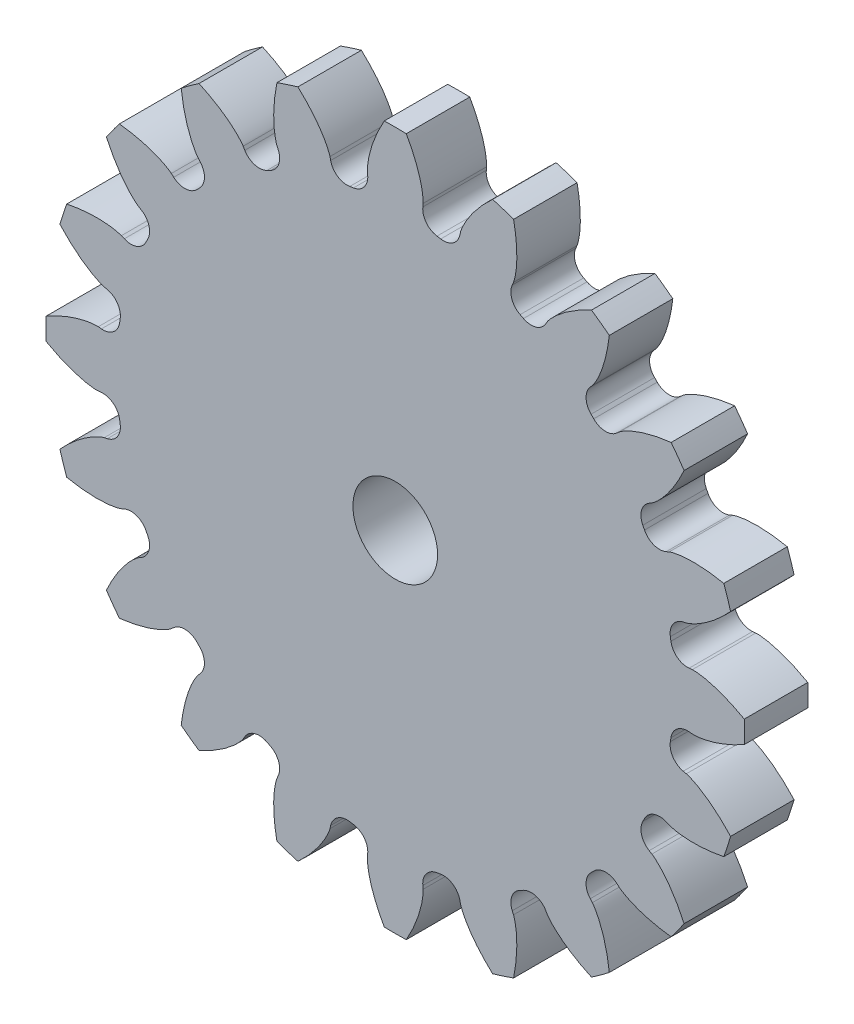
SolidWorks part; units mm, degrees
material "Acrylic (Medium-high impact)"
ref_plane "Front Plane" through (0, 0, 0) normal (0, 0, 1) x (1, 0, 0)
ref_plane "Top Plane" through (0, 0, 0) normal (0, 1, 0) x (1, 0, 0)
ref_plane "Right Plane" through (0, 0, 0) normal (1, 0, 0) x (0, 0, -1)
sketch "Model" plane through (0, 0, 0) normal (0, 0, 1) x (1, 0, 0)
  line L0 (-84.4521, -56.2231) -> (-84.7509, -56.1953)
  line L1 (-84.7509, -61.4561) -> (-84.4521, -61.4283)
  line L2 (-83.8973, -64.9316) -> (-84.19, -64.9974)
  line L3 (-82.5643, -70.0008) -> (-82.2888, -69.882)
  line L4 (-80.6785, -73.0424) -> (-80.9365, -73.1955)
  line L5 (-77.8443, -77.4516) -> (-77.619, -77.2535)
  line L6 (-75.1109, -79.7616) -> (-75.309, -79.9869)
  line L7 (-71.0528, -83.0791) -> (-70.8998, -82.8211)
  line L8 (-67.7394, -84.4314) -> (-67.8582, -84.7069)
  line L9 (-62.8548, -86.3326) -> (-62.789, -86.0399)
  line L10 (-59.2857, -86.5948) -> (-59.3135, -86.8935)
  line L11 (-54.0526, -86.8935) -> (-54.0805, -86.5948)
  line L12 (-50.5772, -86.0399) -> (-50.5113, -86.3326)
  line L13 (-45.508, -84.7069) -> (-45.6268, -84.4314)
  line L14 (-42.4664, -82.8211) -> (-42.3133, -83.0791)
  line L15 (-38.0572, -79.9869) -> (-38.2553, -79.7616)
  line L16 (-35.7472, -77.2535) -> (-35.5219, -77.4516)
  line L17 (-32.4296, -73.1955) -> (-32.6877, -73.0424)
  line L18 (-31.0774, -69.882) -> (-30.8019, -70.0008)
  line L19 (-29.1762, -64.9974) -> (-29.4689, -64.9316)
  line L20 (-28.914, -61.4283) -> (-28.6153, -61.4561)
  line L21 (-28.6153, -56.1953) -> (-28.914, -56.2231)
  line L22 (-29.4689, -52.7198) -> (-29.1762, -52.654)
  line L23 (-30.8019, -47.6506) -> (-31.0774, -47.7694)
  line L24 (-32.6877, -44.609) -> (-32.4296, -44.4559)
  line L25 (-35.5219, -40.1998) -> (-35.7472, -40.3979)
  line L26 (-38.2553, -37.8898) -> (-38.0572, -37.6645)
  line L27 (-42.3133, -34.5722) -> (-42.4664, -34.8303)
  line L28 (-45.6268, -33.22) -> (-45.508, -32.9445)
  line L29 (-50.5113, -31.3188) -> (-50.5772, -31.6115)
  line L30 (-54.0805, -31.0566) -> (-54.0526, -30.7579)
  line L31 (-59.3135, -30.7579) -> (-59.2857, -31.0566)
  line L32 (-62.789, -31.6115) -> (-62.8548, -31.3188)
  line L33 (-67.8582, -32.9445) -> (-67.7394, -33.22)
  line L34 (-70.8998, -34.8303) -> (-71.0528, -34.5722)
  line L35 (-75.309, -37.6645) -> (-75.1109, -37.8898)
  line L36 (-77.619, -40.3979) -> (-77.8443, -40.1998)
  line L37 (-80.9365, -44.4559) -> (-80.6785, -44.609)
  line L38 (-82.2888, -47.7694) -> (-82.5643, -47.6506)
  line L39 (-84.19, -52.654) -> (-83.8973, -52.7198)
  arc A0 (-82.6794, -54.5276) -> (-82.7352, -54.8802) centre (-56.6831, -58.8257) ccw
  arc A1 (-84.4521, -56.2231) -> (-82.7352, -54.8802) centre (-84.3048, -54.6425) ccw
  arc A2 (-89.6666, -57.7836) -> (-89.6666, -59.8678) centre (-56.6831, -58.8257) ccw
  arc A3 (-82.7352, -62.7712) -> (-84.4521, -61.4283) centre (-84.3048, -63.0089) ccw
  arc A4 (-82.7352, -62.7712) -> (-82.6794, -63.1238) centre (-56.6831, -58.8257) ccw
  arc A5 (-83.8973, -64.9316) -> (-82.6794, -63.1238) centre (-84.2456, -63.3828) ccw
  arc A6 (-88.3743, -68.027) -> (-87.7302, -70.0093) centre (-56.6831, -58.8257) ccw
  arc A7 (-80.2409, -70.6287) -> (-82.2888, -69.882) centre (-81.6602, -71.3398) ccw
  arc A8 (-80.2409, -70.6287) -> (-80.0788, -70.9468) centre (-56.6831, -58.8257) ccw
  arc A9 (-80.6785, -73.0424) -> (-80.0788, -70.9468) centre (-81.4884, -71.677) ccw
  arc A10 (-83.9799, -77.3698) -> (-82.7548, -79.0561) centre (-56.6831, -58.8257) ccw
  arc A11 (-75.4406, -77.3307) -> (-77.619, -77.2535) centre (-76.5707, -78.4457) ccw
  arc A12 (-75.4406, -77.3307) -> (-75.1881, -77.5832) centre (-56.6831, -58.8257) ccw
  arc A13 (-75.1109, -79.7616) -> (-75.1881, -77.5832) centre (-76.303, -78.7133) ccw
  arc A14 (-76.9134, -84.8974) -> (-75.2272, -86.1225) centre (-56.6831, -58.8257) ccw
  arc A15 (-68.8041, -82.2214) -> (-70.8998, -82.8211) centre (-69.5344, -83.631) ccw
  arc A16 (-68.8041, -82.2214) -> (-68.486, -82.3835) centre (-56.6831, -58.8257) ccw
  arc A17 (-67.7394, -84.4314) -> (-68.486, -82.3835) centre (-69.1972, -83.8028) ccw
  arc A18 (-67.8667, -89.8729) -> (-65.8844, -90.517) centre (-56.6831, -58.8257) ccw
  arc A19 (-60.9812, -84.822) -> (-62.789, -86.0399) centre (-61.2402, -86.3882) ccw
  arc A20 (-60.9812, -84.822) -> (-60.6286, -84.8778) centre (-56.6831, -58.8257) ccw
  arc A21 (-59.2857, -86.5948) -> (-60.6286, -84.8778) centre (-60.8663, -86.4474) ccw
  arc A22 (-57.7252, -91.8092) -> (-55.6409, -91.8092) centre (-56.6831, -58.8257) ccw
  arc A23 (-52.7376, -84.8778) -> (-54.0805, -86.5948) centre (-52.4998, -86.4474) ccw
  arc A24 (-52.7376, -84.8778) -> (-52.3849, -84.822) centre (-56.6831, -58.8257) ccw
  arc A25 (-50.5772, -86.0399) -> (-52.3849, -84.822) centre (-52.126, -86.3882) ccw
  arc A26 (-47.4817, -90.517) -> (-45.4995, -89.8729) centre (-56.6831, -58.8257) ccw
  arc A27 (-44.8801, -82.3835) -> (-45.6268, -84.4314) centre (-44.169, -83.8028) ccw
  arc A28 (-44.8801, -82.3835) -> (-44.562, -82.2214) centre (-56.6831, -58.8257) ccw
  arc A29 (-42.4664, -82.8211) -> (-44.562, -82.2214) centre (-43.8317, -83.631) ccw
  arc A30 (-38.139, -86.1225) -> (-36.4527, -84.8974) centre (-56.6831, -58.8257) ccw
  arc A31 (-38.178, -77.5832) -> (-38.2553, -79.7616) centre (-37.0631, -78.7133) ccw
  arc A32 (-38.178, -77.5832) -> (-37.9256, -77.3307) centre (-56.6831, -58.8257) ccw
  arc A33 (-35.7472, -77.2535) -> (-37.9256, -77.3307) centre (-36.7955, -78.4457) ccw
  arc A34 (-30.6114, -79.0561) -> (-29.3863, -77.3698) centre (-56.6831, -58.8257) ccw
  arc A35 (-33.2873, -70.9468) -> (-32.6877, -73.0424) centre (-31.8778, -71.677) ccw
  arc A36 (-33.2873, -70.9468) -> (-33.1253, -70.6287) centre (-56.6831, -58.8257) ccw
  arc A37 (-31.0774, -69.882) -> (-33.1253, -70.6287) centre (-31.7059, -71.3398) ccw
  arc A38 (-25.6359, -70.0093) -> (-24.9918, -68.027) centre (-56.6831, -58.8257) ccw
  arc A39 (-30.6868, -63.1238) -> (-29.4689, -64.9316) centre (-29.1206, -63.3828) ccw
  arc A40 (-30.6868, -63.1238) -> (-30.631, -62.7712) centre (-56.6831, -58.8257) ccw
  arc A41 (-28.914, -61.4283) -> (-30.631, -62.7712) centre (-29.0614, -63.0089) ccw
  arc A42 (-23.6995, -59.8678) -> (-23.6995, -57.7836) centre (-56.6831, -58.8257) ccw
  arc A43 (-30.631, -54.8802) -> (-28.914, -56.2231) centre (-29.0614, -54.6425) ccw
  arc A44 (-30.631, -54.8802) -> (-30.6868, -54.5276) centre (-56.6831, -58.8257) ccw
  arc A45 (-29.4689, -52.7198) -> (-30.6868, -54.5276) centre (-29.1206, -54.2686) ccw
  arc A46 (-24.9918, -49.6244) -> (-25.6359, -47.6421) centre (-56.6831, -58.8257) ccw
  arc A47 (-33.1253, -47.0227) -> (-31.0774, -47.7694) centre (-31.7059, -46.3116) ccw
  arc A48 (-33.1253, -47.0227) -> (-33.2873, -46.7046) centre (-56.6831, -58.8257) ccw
  arc A49 (-32.6877, -44.609) -> (-33.2873, -46.7046) centre (-31.8778, -45.9744) ccw
  arc A50 (-29.3863, -40.2816) -> (-30.6114, -38.5953) centre (-56.6831, -58.8257) ccw
  arc A51 (-37.9256, -40.3206) -> (-35.7472, -40.3979) centre (-36.7955, -39.2057) ccw
  arc A52 (-37.9256, -40.3206) -> (-38.178, -40.0682) centre (-56.6831, -58.8257) ccw
  arc A53 (-38.2553, -37.8898) -> (-38.178, -40.0682) centre (-37.0631, -38.9381) ccw
  arc A54 (-36.4527, -32.754) -> (-38.139, -31.5289) centre (-56.6831, -58.8257) ccw
  arc A55 (-44.562, -35.43) -> (-42.4664, -34.8303) centre (-43.8317, -34.0204) ccw
  arc A56 (-44.562, -35.43) -> (-44.8801, -35.2679) centre (-56.6831, -58.8257) ccw
  arc A57 (-45.6268, -33.22) -> (-44.8801, -35.2679) centre (-44.169, -33.8486) ccw
  arc A58 (-45.4995, -27.7785) -> (-47.4817, -27.1344) centre (-56.6831, -58.8257) ccw
  arc A59 (-52.3849, -32.8294) -> (-50.5772, -31.6115) centre (-52.126, -31.2632) ccw
  arc A60 (-52.3849, -32.8294) -> (-52.7376, -32.7736) centre (-56.6831, -58.8257) ccw
  arc A61 (-54.0805, -31.0566) -> (-52.7376, -32.7736) centre (-52.4998, -31.204) ccw
  arc A62 (-55.6409, -25.8422) -> (-57.7252, -25.8422) centre (-56.6831, -58.8257) ccw
  arc A63 (-60.6286, -32.7736) -> (-59.2857, -31.0566) centre (-60.8663, -31.204) ccw
  arc A64 (-60.6286, -32.7736) -> (-60.9812, -32.8294) centre (-56.6831, -58.8257) ccw
  arc A65 (-62.789, -31.6115) -> (-60.9812, -32.8294) centre (-61.2402, -31.2632) ccw
  arc A66 (-65.8844, -27.1344) -> (-67.8667, -27.7785) centre (-56.6831, -58.8257) ccw
  arc A67 (-68.486, -35.2679) -> (-67.7394, -33.22) centre (-69.1972, -33.8486) ccw
  arc A68 (-68.486, -35.2679) -> (-68.8041, -35.43) centre (-56.6831, -58.8257) ccw
  arc A69 (-70.8998, -34.8303) -> (-68.8041, -35.43) centre (-69.5344, -34.0204) ccw
  arc A70 (-75.2272, -31.5289) -> (-76.9134, -32.754) centre (-56.6831, -58.8257) ccw
  arc A71 (-75.1881, -40.0682) -> (-75.1109, -37.8898) centre (-76.303, -38.9381) ccw
  arc A72 (-75.1881, -40.0682) -> (-75.4406, -40.3206) centre (-56.6831, -58.8257) ccw
  arc A73 (-77.619, -40.3979) -> (-75.4406, -40.3206) centre (-76.5707, -39.2057) ccw
  arc A74 (-82.7548, -38.5953) -> (-83.9799, -40.2816) centre (-56.6831, -58.8257) ccw
  arc A75 (-80.0788, -46.7046) -> (-80.6785, -44.609) centre (-81.4884, -45.9744) ccw
  arc A76 (-80.0788, -46.7046) -> (-80.2409, -47.0227) centre (-56.6831, -58.8257) ccw
  arc A77 (-82.2888, -47.7694) -> (-80.2409, -47.0227) centre (-81.6602, -46.3116) ccw
  arc A78 (-87.7302, -47.6421) -> (-88.3743, -49.6244) centre (-56.6831, -58.8257) ccw
  arc A79 (-82.6794, -54.5276) -> (-83.8973, -52.7198) centre (-84.2456, -54.2686) ccw
  circle A80 centre (-56.6831, -58.8257) radius 4
  spline S0 degree 5 poles (-84.7509, -56.1953) (-84.8074, -56.19) (-84.8782, -56.1872) (-84.9775, -56.1898) (-85.1055, -56.1991) (-85.2478, -56.2118) (-85.3901, -56.2258) (-85.5326, -56.2436) (-85.7035, -56.2705) (-85.8744, -56.302) (-86.0736, -56.3427) (-86.2727, -56.3877) (-86.4858, -56.4423) (-86.6986, -56.5012) (-86.9677, -56.5821) (-87.2645, -56.6802) (-87.5744, -56.7917) (-87.9393, -56.9353) (-88.3163, -57.097) (-88.6776, -57.264) (-89.023, -57.4349) (-89.2978, -57.5793) (-89.4893, -57.6839) (-89.6121, -57.7527) (-89.6666, -57.7836) knots 0 0 0 0 0 0 0.057143 0.071429 0.1 0.128571 0.142857 0.2 0.214286 0.271429 0.3 0.342857 0.4 0.428571 0.485714 0.571429 0.642857 0.714286 0.8 0.871429 0.942857 1 1 1 1 1 1 weights 1 1 1 1 1 1 1 1 1 1 1 1 1 1 1 1 1 1 1 1 1 1 1 1 1
  spline S1 degree 5 poles (-89.6666, -59.8678) (-89.4895, -59.9681) (-89.2569, -60.0952) (-88.9681, -60.2456) (-88.6085, -60.4214) (-88.1768, -60.6148) (-87.8691, -60.7439) (-87.5462, -60.8698) (-87.2362, -60.9808) (-86.9677, -61.0691) (-86.7128, -61.1462) (-86.5, -61.2051) (-86.3012, -61.2564) (-86.1305, -61.2962) (-85.9598, -61.3321) (-85.8032, -61.3627) (-85.6465, -61.39) (-85.5041, -61.4118) (-85.3617, -61.4286) (-85.2193, -61.4422) (-85.077, -61.4547) (-84.9491, -61.4627) (-84.864, -61.4639) (-84.7933, -61.4601) (-84.7509, -61.4561) knots -1 -1 -1 -1 -1 -1 -0.814286 -0.757143 -0.7 -0.628571 -0.557143 -0.5 -0.428571 -0.385714 -0.357143 -0.3 -0.285714 -0.228571 -0.214286 -0.185714 -0.142857 -0.128571 -0.085714 -0.071429 -0.042857 0 0 0 0 0 0 weights 1 1 1 1 1 1 1 1 1 1 1 1 1 1 1 1 1 1 1 1 1 1 1 1 1
  spline S2 degree 5 poles (-84.19, -64.9974) (-84.2454, -65.0099) (-84.3136, -65.0291) (-84.4072, -65.0622) (-84.526, -65.1107) (-84.6575, -65.1667) (-84.7885, -65.224) (-84.9185, -65.2849) (-85.0727, -65.3633) (-85.2255, -65.4461) (-85.4025, -65.5464) (-85.5779, -65.6508) (-85.7637, -65.7685) (-85.9479, -65.8903) (-86.1788, -66.0504) (-86.4307, -66.2354) (-86.691, -66.4372) (-86.9937, -66.6865) (-87.3023, -66.9568) (-87.5943, -67.2273) (-87.87, -67.4966) (-88.0867, -67.7188) (-88.2365, -67.8775) (-88.332, -67.9808) (-88.3743, -68.027) knots 0 0 0 0 0 0 0.057143 0.071429 0.1 0.128571 0.142857 0.2 0.214286 0.271429 0.3 0.342857 0.4 0.428571 0.485714 0.571429 0.642857 0.714286 0.8 0.871429 0.942857 1 1 1 1 1 1 weights 1 1 1 1 1 1 1 1 1 1 1 1 1 1 1 1 1 1 1 1 1 1 1 1 1
  spline S3 degree 5 poles (-87.7302, -70.0093) (-87.5308, -70.0499) (-87.2704, -70.0989) (-86.9492, -70.1528) (-86.5528, -70.2088) (-86.0825, -70.2594) (-85.75, -70.287) (-85.404, -70.307) (-85.0749, -70.3167) (-84.7922, -70.3178) (-84.526, -70.3123) (-84.3054, -70.3026) (-84.1004, -70.2899) (-83.9258, -70.275) (-83.7523, -70.2564) (-83.5939, -70.2372) (-83.4365, -70.2147) (-83.2943, -70.1914) (-83.1537, -70.1634) (-83.0141, -70.1323) (-82.8749, -70.1002) (-82.7508, -70.0684) (-82.6695, -70.0431) (-82.6034, -70.0177) (-82.5643, -70.0008) knots -1 -1 -1 -1 -1 -1 -0.814286 -0.757143 -0.7 -0.628571 -0.557143 -0.5 -0.428571 -0.385714 -0.357143 -0.3 -0.285714 -0.228571 -0.214286 -0.185714 -0.142857 -0.128571 -0.085714 -0.071429 -0.042857 0 0 0 0 0 0 weights 1 1 1 1 1 1 1 1 1 1 1 1 1 1 1 1 1 1 1 1 1 1 1 1 1
  spline S4 degree 5 poles (-80.9365, -73.1955) (-80.9853, -73.2244) (-81.0443, -73.2637) (-81.1231, -73.3242) (-81.2211, -73.407) (-81.3288, -73.5009) (-81.4357, -73.5959) (-81.5405, -73.694) (-81.663, -73.8162) (-81.7827, -73.9422) (-81.92, -74.0922) (-82.0546, -74.2457) (-82.1949, -74.4151) (-82.3325, -74.5878) (-82.5026, -74.8115) (-82.685, -75.0653) (-82.8703, -75.3376) (-83.081, -75.6682) (-83.291, -76.0207) (-83.4851, -76.3682) (-83.6641, -76.7095) (-83.8016, -76.9878) (-83.895, -77.185) (-83.9539, -77.3128) (-83.9799, -77.3698) knots 0 0 0 0 0 0 0.057143 0.071429 0.1 0.128571 0.142857 0.2 0.214286 0.271429 0.3 0.342857 0.4 0.428571 0.485714 0.571429 0.642857 0.714286 0.8 0.871429 0.942857 1 1 1 1 1 1 weights 1 1 1 1 1 1 1 1 1 1 1 1 1 1 1 1 1 1 1 1 1 1 1 1 1
  spline S5 degree 5 poles (-82.7548, -79.0561) (-82.5525, -79.0331) (-82.2897, -78.9992) (-81.9676, -78.9511) (-81.5733, -78.8819) (-81.1104, -78.7847) (-80.7856, -78.7082) (-80.4504, -78.6203) (-80.1344, -78.5279) (-79.8652, -78.4415) (-79.6137, -78.3541) (-79.4069, -78.2766) (-79.2159, -78.2012) (-79.0544, -78.1331) (-78.8952, -78.0618) (-78.7505, -77.9946) (-78.6077, -77.9246) (-78.4797, -77.8585) (-78.3546, -77.7883) (-78.2314, -77.7157) (-78.109, -77.6421) (-78.0008, -77.5735) (-77.9313, -77.5243) (-77.8762, -77.4797) (-77.8443, -77.4516) knots -1 -1 -1 -1 -1 -1 -0.814286 -0.757143 -0.7 -0.628571 -0.557143 -0.5 -0.428571 -0.385714 -0.357143 -0.3 -0.285714 -0.228571 -0.214286 -0.185714 -0.142857 -0.128571 -0.085714 -0.071429 -0.042857 0 0 0 0 0 0 weights 1 1 1 1 1 1 1 1 1 1 1 1 1 1 1 1 1 1 1 1 1 1 1 1 1
  spline S6 degree 5 poles (-75.309, -79.9869) (-75.3465, -80.0295) (-75.3904, -80.0851) (-75.4466, -80.167) (-75.5143, -80.276) (-75.5877, -80.3986) (-75.66, -80.522) (-75.7294, -80.6477) (-75.8081, -80.8018) (-75.883, -80.9586) (-75.9672, -81.1437) (-76.0478, -81.3312) (-76.1289, -81.5357) (-76.2063, -81.7425) (-76.2991, -82.0078) (-76.3941, -82.3055) (-76.4861, -82.6217) (-76.5844, -83.0013) (-76.6752, -83.4015) (-76.7524, -83.7919) (-76.8172, -84.1718) (-76.8619, -84.479) (-76.8898, -84.6954) (-76.9064, -84.8352) (-76.9134, -84.8974) knots 0 0 0 0 0 0 0.057143 0.071429 0.1 0.128571 0.142857 0.2 0.214286 0.271429 0.3 0.342857 0.4 0.428571 0.485714 0.571429 0.642857 0.714286 0.8 0.871429 0.942857 1 1 1 1 1 1 weights 1 1 1 1 1 1 1 1 1 1 1 1 1 1 1 1 1 1 1 1 1 1 1 1 1
  spline S7 degree 5 poles (-75.2272, -86.1225) (-75.042, -86.0381) (-74.8025, -85.9247) (-74.511, -85.7795) (-74.1574, -85.5918) (-73.7472, -85.3563) (-73.4619, -85.1832) (-73.1702, -84.996) (-72.8983, -84.8104) (-72.669, -84.6451) (-72.4568, -84.4842) (-72.2841, -84.3467) (-72.1257, -84.2159) (-71.9932, -84.1013) (-71.8638, -83.9843) (-71.7469, -83.8756) (-71.6328, -83.7649) (-71.5314, -83.6625) (-71.4341, -83.5571) (-71.3394, -83.4499) (-71.2457, -83.3422) (-71.164, -83.2434) (-71.1131, -83.1752) (-71.0746, -83.1158) (-71.0528, -83.0791) knots -1 -1 -1 -1 -1 -1 -0.814286 -0.757143 -0.7 -0.628571 -0.557143 -0.5 -0.428571 -0.385714 -0.357143 -0.3 -0.285714 -0.228571 -0.214286 -0.185714 -0.142857 -0.128571 -0.085714 -0.071429 -0.042857 0 0 0 0 0 0 weights 1 1 1 1 1 1 1 1 1 1 1 1 1 1 1 1 1 1 1 1 1 1 1 1 1
  spline S8 degree 5 poles (-67.8582, -84.7069) (-67.8807, -84.759) (-67.9052, -84.8255) (-67.9334, -84.9207) (-67.9641, -85.0453) (-67.996, -85.1846) (-68.0267, -85.3243) (-68.0538, -85.4653) (-68.0811, -85.6361) (-68.1039, -85.8084) (-68.1268, -86.0105) (-68.1454, -86.2138) (-68.1594, -86.4333) (-68.1691, -86.6539) (-68.1753, -86.9348) (-68.1737, -87.2473) (-68.1635, -87.5765) (-68.1397, -87.9679) (-68.1024, -88.3765) (-68.0552, -88.7717) (-67.9994, -89.1531) (-67.947, -89.459) (-67.9066, -89.6735) (-67.8792, -89.8115) (-67.8667, -89.8729) knots 0 0 0 0 0 0 0.057143 0.071429 0.1 0.128571 0.142857 0.2 0.214286 0.271429 0.3 0.342857 0.4 0.428571 0.485714 0.571429 0.642857 0.714286 0.8 0.871429 0.942857 1 1 1 1 1 1 weights 1 1 1 1 1 1 1 1 1 1 1 1 1 1 1 1 1 1 1 1 1 1 1 1 1
  spline S9 degree 5 poles (-65.8844, -90.517) (-65.7343, -90.3795) (-65.5416, -90.1976) (-65.3093, -89.9694) (-65.0309, -89.6817) (-64.7136, -89.3309) (-64.4958, -89.0781) (-64.2762, -88.81) (-64.0749, -88.5494) (-63.908, -88.3214) (-63.7559, -88.1028) (-63.6341, -87.9185) (-63.5239, -87.7453) (-63.4333, -87.5953) (-63.3463, -87.444) (-63.2688, -87.3045) (-63.1944, -87.164) (-63.1297, -87.0352) (-63.0697, -86.905) (-63.0128, -86.7738) (-62.957, -86.6423) (-62.9098, -86.5232) (-62.8824, -86.4426) (-62.8642, -86.3741) (-62.8548, -86.3326) knots -1 -1 -1 -1 -1 -1 -0.814286 -0.757143 -0.7 -0.628571 -0.557143 -0.5 -0.428571 -0.385714 -0.357143 -0.3 -0.285714 -0.228571 -0.214286 -0.185714 -0.142857 -0.128571 -0.085714 -0.071429 -0.042857 0 0 0 0 0 0 weights 1 1 1 1 1 1 1 1 1 1 1 1 1 1 1 1 1 1 1 1 1 1 1 1 1
  spline S10 degree 5 poles (-59.3135, -86.8935) (-59.3188, -86.95) (-59.3216, -87.0208) (-59.319, -87.1201) (-59.3097, -87.2481) (-59.297, -87.3904) (-59.283, -87.5328) (-59.2652, -87.6752) (-59.2383, -87.8461) (-59.2068, -88.017) (-59.1661, -88.2162) (-59.121, -88.4154) (-59.0665, -88.6284) (-59.0076, -88.8413) (-58.9267, -89.1104) (-58.8286, -89.4071) (-58.7171, -89.717) (-58.5735, -90.0819) (-58.4118, -90.459) (-58.2447, -90.8202) (-58.0738, -91.1657) (-57.9295, -91.4404) (-57.8248, -91.632) (-57.7561, -91.7547) (-57.7252, -91.8092) knots 0 0 0 0 0 0 0.057143 0.071429 0.1 0.128571 0.142857 0.2 0.214286 0.271429 0.3 0.342857 0.4 0.428571 0.485714 0.571429 0.642857 0.714286 0.8 0.871429 0.942857 1 1 1 1 1 1 weights 1 1 1 1 1 1 1 1 1 1 1 1 1 1 1 1 1 1 1 1 1 1 1 1 1
  spline S11 degree 5 poles (-55.6409, -91.8092) (-55.5407, -91.6321) (-55.4136, -91.3996) (-55.2631, -91.1107) (-55.0874, -90.7511) (-54.8939, -90.3194) (-54.7649, -90.0117) (-54.6389, -89.6888) (-54.528, -89.3788) (-54.4397, -89.1103) (-54.3626, -88.8554) (-54.3037, -88.6426) (-54.2524, -88.4438) (-54.2126, -88.2731) (-54.1767, -88.1024) (-54.1461, -87.9458) (-54.1188, -87.7891) (-54.097, -87.6467) (-54.0802, -87.5043) (-54.0666, -87.3619) (-54.0541, -87.2196) (-54.046, -87.0917) (-54.0449, -87.0066) (-54.0487, -86.9359) (-54.0526, -86.8935) knots -1 -1 -1 -1 -1 -1 -0.814286 -0.757143 -0.7 -0.628571 -0.557143 -0.5 -0.428571 -0.385714 -0.357143 -0.3 -0.285714 -0.228571 -0.214286 -0.185714 -0.142857 -0.128571 -0.085714 -0.071429 -0.042857 0 0 0 0 0 0 weights 1 1 1 1 1 1 1 1 1 1 1 1 1 1 1 1 1 1 1 1 1 1 1 1 1
  spline S12 degree 5 poles (-50.5113, -86.3326) (-50.4989, -86.388) (-50.4797, -86.4562) (-50.4465, -86.5498) (-50.3981, -86.6686) (-50.342, -86.8001) (-50.2847, -86.9311) (-50.2239, -87.0611) (-50.1455, -87.2154) (-50.0626, -87.3681) (-49.9624, -87.5451) (-49.858, -87.7205) (-49.7402, -87.9063) (-49.6185, -88.0905) (-49.4584, -88.3214) (-49.2734, -88.5733) (-49.0716, -88.8336) (-48.8223, -89.1363) (-48.5519, -89.4449) (-48.2815, -89.7369) (-48.0122, -90.0126) (-47.79, -90.2293) (-47.6313, -90.3791) (-47.5279, -90.4747) (-47.4817, -90.517) knots 0 0 0 0 0 0 0.057143 0.071429 0.1 0.128571 0.142857 0.2 0.214286 0.271429 0.3 0.342857 0.4 0.428571 0.485714 0.571429 0.642857 0.714286 0.8 0.871429 0.942857 1 1 1 1 1 1 weights 1 1 1 1 1 1 1 1 1 1 1 1 1 1 1 1 1 1 1 1 1 1 1 1 1
  spline S13 degree 5 poles (-45.4995, -89.8729) (-45.4588, -89.6734) (-45.4098, -89.413) (-45.356, -89.0918) (-45.3, -88.6954) (-45.2494, -88.2251) (-45.2218, -87.8926) (-45.2018, -87.5466) (-45.192, -87.2175) (-45.191, -86.9349) (-45.1965, -86.6686) (-45.2062, -86.448) (-45.2189, -86.243) (-45.2337, -86.0685) (-45.2523, -85.895) (-45.2716, -85.7366) (-45.2941, -85.5791) (-45.3173, -85.4369) (-45.3454, -85.2963) (-45.3764, -85.1567) (-45.4085, -85.0175) (-45.4404, -84.8934) (-45.4657, -84.8121) (-45.4911, -84.746) (-45.508, -84.7069) knots -1 -1 -1 -1 -1 -1 -0.814286 -0.757143 -0.7 -0.628571 -0.557143 -0.5 -0.428571 -0.385714 -0.357143 -0.3 -0.285714 -0.228571 -0.214286 -0.185714 -0.142857 -0.128571 -0.085714 -0.071429 -0.042857 0 0 0 0 0 0 weights 1 1 1 1 1 1 1 1 1 1 1 1 1 1 1 1 1 1 1 1 1 1 1 1 1
  spline S14 degree 5 poles (-42.3133, -83.0791) (-42.2844, -83.128) (-42.245, -83.1869) (-42.1845, -83.2657) (-42.1018, -83.3637) (-42.0078, -83.4714) (-41.9128, -83.5784) (-41.8148, -83.6832) (-41.6926, -83.8056) (-41.5666, -83.9253) (-41.4166, -84.0626) (-41.2631, -84.1972) (-41.0937, -84.3375) (-40.9209, -84.4751) (-40.6973, -84.6453) (-40.4435, -84.8276) (-40.1712, -85.0129) (-39.8405, -85.2237) (-39.488, -85.4336) (-39.1406, -85.6277) (-38.7993, -85.8067) (-38.521, -85.9442) (-38.3237, -86.0376) (-38.1959, -86.0965) (-38.139, -86.1225) knots 0 0 0 0 0 0 0.057143 0.071429 0.1 0.128571 0.142857 0.2 0.214286 0.271429 0.3 0.342857 0.4 0.428571 0.485714 0.571429 0.642857 0.714286 0.8 0.871429 0.942857 1 1 1 1 1 1 weights 1 1 1 1 1 1 1 1 1 1 1 1 1 1 1 1 1 1 1 1 1 1 1 1 1
  spline S15 degree 5 poles (-36.4527, -84.8974) (-36.4757, -84.6951) (-36.5096, -84.4323) (-36.5576, -84.1102) (-36.6268, -83.7159) (-36.7241, -83.253) (-36.8006, -82.9283) (-36.8884, -82.593) (-36.9809, -82.277) (-37.0673, -82.0079) (-37.1547, -81.7563) (-37.2322, -81.5495) (-37.3076, -81.3585) (-37.3756, -81.1971) (-37.4469, -81.0378) (-37.5142, -80.8931) (-37.5842, -80.7503) (-37.6503, -80.6223) (-37.7204, -80.4972) (-37.7931, -80.374) (-37.8666, -80.2516) (-37.9353, -80.1434) (-37.9844, -80.0739) (-38.0291, -80.0189) (-38.0572, -79.9869) knots -1 -1 -1 -1 -1 -1 -0.814286 -0.757143 -0.7 -0.628571 -0.557143 -0.5 -0.428571 -0.385714 -0.357143 -0.3 -0.285714 -0.228571 -0.214286 -0.185714 -0.142857 -0.128571 -0.085714 -0.071429 -0.042857 0 0 0 0 0 0 weights 1 1 1 1 1 1 1 1 1 1 1 1 1 1 1 1 1 1 1 1 1 1 1 1 1
  spline S16 degree 5 poles (-35.5219, -77.4516) (-35.4793, -77.4891) (-35.4237, -77.533) (-35.3418, -77.5892) (-35.2328, -77.6569) (-35.1102, -77.7303) (-34.9867, -77.8026) (-34.8611, -77.872) (-34.707, -77.9507) (-34.5502, -78.0256) (-34.3651, -78.1098) (-34.1775, -78.1904) (-33.9731, -78.2715) (-33.7663, -78.349) (-33.501, -78.4417) (-33.2033, -78.5367) (-32.887, -78.6287) (-32.5075, -78.727) (-32.1073, -78.8178) (-31.7169, -78.895) (-31.337, -78.9598) (-31.0298, -79.0045) (-30.8134, -79.0324) (-30.6736, -79.049) (-30.6114, -79.0561) knots 0 0 0 0 0 0 0.057143 0.071429 0.1 0.128571 0.142857 0.2 0.214286 0.271429 0.3 0.342857 0.4 0.428571 0.485714 0.571429 0.642857 0.714286 0.8 0.871429 0.942857 1 1 1 1 1 1 weights 1 1 1 1 1 1 1 1 1 1 1 1 1 1 1 1 1 1 1 1 1 1 1 1 1
  spline S17 degree 5 poles (-29.3863, -77.3698) (-29.4706, -77.1846) (-29.5841, -76.9451) (-29.7293, -76.6536) (-29.917, -76.3) (-30.1525, -75.8898) (-30.3256, -75.6046) (-30.5128, -75.3129) (-30.6983, -75.0409) (-30.8637, -74.8116) (-31.0246, -74.5994) (-31.1621, -74.4267) (-31.2929, -74.2683) (-31.4075, -74.1358) (-31.5245, -74.0064) (-31.6332, -73.8896) (-31.7439, -73.7754) (-31.8463, -73.674) (-31.9517, -73.5768) (-32.0588, -73.4821) (-32.1666, -73.3883) (-32.2654, -73.3066) (-32.3336, -73.2557) (-32.393, -73.2172) (-32.4296, -73.1955) knots -1 -1 -1 -1 -1 -1 -0.814286 -0.757143 -0.7 -0.628571 -0.557143 -0.5 -0.428571 -0.385714 -0.357143 -0.3 -0.285714 -0.228571 -0.214286 -0.185714 -0.142857 -0.128571 -0.085714 -0.071429 -0.042857 0 0 0 0 0 0 weights 1 1 1 1 1 1 1 1 1 1 1 1 1 1 1 1 1 1 1 1 1 1 1 1 1
  spline S18 degree 5 poles (-30.8019, -70.0008) (-30.7497, -70.0233) (-30.6833, -70.0479) (-30.588, -70.0761) (-30.4634, -70.1067) (-30.3242, -70.1386) (-30.1844, -70.1693) (-30.0435, -70.1964) (-29.8727, -70.2237) (-29.7004, -70.2465) (-29.4983, -70.2694) (-29.295, -70.288) (-29.0755, -70.302) (-28.8549, -70.3117) (-28.574, -70.318) (-28.2614, -70.3163) (-27.9322, -70.3061) (-27.5408, -70.2823) (-27.1323, -70.245) (-26.7371, -70.1978) (-26.3557, -70.142) (-26.0498, -70.0896) (-25.8353, -70.0493) (-25.6973, -70.0218) (-25.6359, -70.0093) knots 0 0 0 0 0 0 0.057143 0.071429 0.1 0.128571 0.142857 0.2 0.214286 0.271429 0.3 0.342857 0.4 0.428571 0.485714 0.571429 0.642857 0.714286 0.8 0.871429 0.942857 1 1 1 1 1 1 weights 1 1 1 1 1 1 1 1 1 1 1 1 1 1 1 1 1 1 1 1 1 1 1 1 1
  spline S19 degree 5 poles (-24.9918, -68.027) (-25.1293, -67.8769) (-25.3112, -67.6842) (-25.5394, -67.4519) (-25.8271, -67.1736) (-26.1779, -66.8562) (-26.4307, -66.6384) (-26.6988, -66.4188) (-26.9593, -66.2175) (-27.1874, -66.0506) (-27.406, -65.8985) (-27.5902, -65.7767) (-27.7635, -65.6665) (-27.9135, -65.5759) (-28.0648, -65.4889) (-28.2042, -65.4114) (-28.3448, -65.3371) (-28.4735, -65.2723) (-28.6038, -65.2124) (-28.735, -65.1554) (-28.8664, -65.0996) (-28.9856, -65.0524) (-29.0662, -65.0251) (-29.1346, -65.0068) (-29.1762, -64.9974) knots -1 -1 -1 -1 -1 -1 -0.814286 -0.757143 -0.7 -0.628571 -0.557143 -0.5 -0.428571 -0.385714 -0.357143 -0.3 -0.285714 -0.228571 -0.214286 -0.185714 -0.142857 -0.128571 -0.085714 -0.071429 -0.042857 0 0 0 0 0 0 weights 1 1 1 1 1 1 1 1 1 1 1 1 1 1 1 1 1 1 1 1 1 1 1 1 1
  spline S20 degree 5 poles (-28.6153, -61.4561) (-28.5588, -61.4614) (-28.488, -61.4642) (-28.3887, -61.4616) (-28.2607, -61.4523) (-28.1184, -61.4396) (-27.976, -61.4256) (-27.8336, -61.4078) (-27.6627, -61.3809) (-27.4918, -61.3494) (-27.2925, -61.3087) (-27.0934, -61.2637) (-26.8803, -61.2091) (-26.6675, -61.1502) (-26.3984, -61.0693) (-26.1017, -60.9712) (-25.7918, -60.8597) (-25.4269, -60.7161) (-25.0498, -60.5544) (-24.6886, -60.3874) (-24.3431, -60.2165) (-24.0683, -60.0721) (-23.8768, -59.9675) (-23.754, -59.8987) (-23.6995, -59.8678) knots 0 0 0 0 0 0 0.057143 0.071429 0.1 0.128571 0.142857 0.2 0.214286 0.271429 0.3 0.342857 0.4 0.428571 0.485714 0.571429 0.642857 0.714286 0.8 0.871429 0.942857 1 1 1 1 1 1 weights 1 1 1 1 1 1 1 1 1 1 1 1 1 1 1 1 1 1 1 1 1 1 1 1 1
  spline S21 degree 5 poles (-23.6995, -57.7836) (-23.8767, -57.6833) (-24.1092, -57.5562) (-24.398, -57.4057) (-24.7577, -57.23) (-25.1894, -57.0365) (-25.497, -56.9075) (-25.8199, -56.7816) (-26.1299, -56.6706) (-26.3984, -56.5823) (-26.6533, -56.5052) (-26.8661, -56.4463) (-27.065, -56.395) (-27.2356, -56.3552) (-27.4064, -56.3193) (-27.563, -56.2887) (-27.7197, -56.2614) (-27.8621, -56.2396) (-28.0045, -56.2228) (-28.1469, -56.2092) (-28.2892, -56.1967) (-28.4171, -56.1887) (-28.5021, -56.1875) (-28.5729, -56.1913) (-28.6153, -56.1953) knots -1 -1 -1 -1 -1 -1 -0.814286 -0.757143 -0.7 -0.628571 -0.557143 -0.5 -0.428571 -0.385714 -0.357143 -0.3 -0.285714 -0.228571 -0.214286 -0.185714 -0.142857 -0.128571 -0.085714 -0.071429 -0.042857 0 0 0 0 0 0 weights 1 1 1 1 1 1 1 1 1 1 1 1 1 1 1 1 1 1 1 1 1 1 1 1 1
  spline S22 degree 5 poles (-29.1762, -52.654) (-29.1208, -52.6415) (-29.0526, -52.6223) (-28.9589, -52.5892) (-28.8401, -52.5407) (-28.7087, -52.4847) (-28.5776, -52.4274) (-28.4477, -52.3665) (-28.2934, -52.2881) (-28.1406, -52.2053) (-27.9637, -52.105) (-27.7883, -52.0006) (-27.6025, -51.8829) (-27.4183, -51.7611) (-27.1873, -51.601) (-26.9355, -51.416) (-26.6751, -51.2142) (-26.3725, -50.9649) (-26.0639, -50.6946) (-25.7719, -50.4241) (-25.4962, -50.1548) (-25.2794, -49.9326) (-25.1296, -49.7739) (-25.0341, -49.6705) (-24.9918, -49.6244) knots 0 0 0 0 0 0 0.057143 0.071429 0.1 0.128571 0.142857 0.2 0.214286 0.271429 0.3 0.342857 0.4 0.428571 0.485714 0.571429 0.642857 0.714286 0.8 0.871429 0.942857 1 1 1 1 1 1 weights 1 1 1 1 1 1 1 1 1 1 1 1 1 1 1 1 1 1 1 1 1 1 1 1 1
  spline S23 degree 5 poles (-25.6359, -47.6421) (-25.8354, -47.6015) (-26.0958, -47.5525) (-26.417, -47.4986) (-26.8133, -47.4426) (-27.2837, -47.392) (-27.6161, -47.3644) (-27.9622, -47.3444) (-28.2913, -47.3347) (-28.5739, -47.3336) (-28.8402, -47.3391) (-29.0608, -47.3488) (-29.2657, -47.3615) (-29.4403, -47.3764) (-29.6138, -47.395) (-29.7722, -47.4142) (-29.9296, -47.4367) (-30.0718, -47.46) (-30.2125, -47.488) (-30.3521, -47.5191) (-30.4913, -47.5512) (-30.6154, -47.583) (-30.6967, -47.6083) (-30.7628, -47.6337) (-30.8019, -47.6506) knots -1 -1 -1 -1 -1 -1 -0.814286 -0.757143 -0.7 -0.628571 -0.557143 -0.5 -0.428571 -0.385714 -0.357143 -0.3 -0.285714 -0.228571 -0.214286 -0.185714 -0.142857 -0.128571 -0.085714 -0.071429 -0.042857 0 0 0 0 0 0 weights 1 1 1 1 1 1 1 1 1 1 1 1 1 1 1 1 1 1 1 1 1 1 1 1 1
  spline S24 degree 5 poles (-32.4296, -44.4559) (-32.3808, -44.427) (-32.3219, -44.3877) (-32.2431, -44.3272) (-32.145, -44.2444) (-32.0374, -44.1505) (-31.9304, -44.0555) (-31.8256, -43.9574) (-31.7031, -43.8352) (-31.5834, -43.7092) (-31.4461, -43.5592) (-31.3115, -43.4057) (-31.1712, -43.2363) (-31.0337, -43.0635) (-30.8635, -42.8399) (-30.6811, -42.5861) (-30.4959, -42.3138) (-30.2851, -41.9832) (-30.0751, -41.6307) (-29.881, -41.2832) (-29.702, -40.9419) (-29.5646, -40.6636) (-29.4711, -40.4664) (-29.4122, -40.3386) (-29.3863, -40.2816) knots 0 0 0 0 0 0 0.057143 0.071429 0.1 0.128571 0.142857 0.2 0.214286 0.271429 0.3 0.342857 0.4 0.428571 0.485714 0.571429 0.642857 0.714286 0.8 0.871429 0.942857 1 1 1 1 1 1 weights 1 1 1 1 1 1 1 1 1 1 1 1 1 1 1 1 1 1 1 1 1 1 1 1 1
  spline S25 degree 5 poles (-30.6114, -38.5953) (-30.8136, -38.6183) (-31.0765, -38.6522) (-31.3986, -38.7003) (-31.7928, -38.7695) (-32.2558, -38.8667) (-32.5805, -38.9432) (-32.9158, -39.0311) (-33.2318, -39.1235) (-33.5009, -39.2099) (-33.7525, -39.2973) (-33.9592, -39.3748) (-34.1503, -39.4502) (-34.3117, -39.5183) (-34.471, -39.5896) (-34.6157, -39.6568) (-34.7584, -39.7268) (-34.8865, -39.7929) (-35.0116, -39.8631) (-35.1347, -39.9357) (-35.2572, -40.0093) (-35.3654, -40.0779) (-35.4349, -40.1271) (-35.4899, -40.1717) (-35.5219, -40.1998) knots -1 -1 -1 -1 -1 -1 -0.814286 -0.757143 -0.7 -0.628571 -0.557143 -0.5 -0.428571 -0.385714 -0.357143 -0.3 -0.285714 -0.228571 -0.214286 -0.185714 -0.142857 -0.128571 -0.085714 -0.071429 -0.042857 0 0 0 0 0 0 weights 1 1 1 1 1 1 1 1 1 1 1 1 1 1 1 1 1 1 1 1 1 1 1 1 1
  spline S26 degree 5 poles (-38.0572, -37.6645) (-38.0197, -37.6219) (-37.9758, -37.5663) (-37.9195, -37.4844) (-37.8519, -37.3754) (-37.7785, -37.2528) (-37.7062, -37.1294) (-37.6368, -37.0037) (-37.5581, -36.8496) (-37.4832, -36.6928) (-37.3989, -36.5077) (-37.3184, -36.3202) (-37.2373, -36.1157) (-37.1598, -35.9089) (-37.0671, -35.6436) (-36.9721, -35.3459) (-36.8801, -35.0297) (-36.7818, -34.6501) (-36.691, -34.2499) (-36.6138, -33.8595) (-36.549, -33.4796) (-36.5042, -33.1724) (-36.4763, -32.956) (-36.4598, -32.8162) (-36.4527, -32.754) knots 0 0 0 0 0 0 0.057143 0.071429 0.1 0.128571 0.142857 0.2 0.214286 0.271429 0.3 0.342857 0.4 0.428571 0.485714 0.571429 0.642857 0.714286 0.8 0.871429 0.942857 1 1 1 1 1 1 weights 1 1 1 1 1 1 1 1 1 1 1 1 1 1 1 1 1 1 1 1 1 1 1 1 1
  spline S27 degree 5 poles (-38.139, -31.5289) (-38.3242, -31.6133) (-38.5637, -31.7267) (-38.8552, -31.8719) (-39.2088, -32.0596) (-39.619, -32.2951) (-39.9042, -32.4682) (-40.1959, -32.6554) (-40.4679, -32.841) (-40.6971, -33.0063) (-40.9094, -33.1672) (-41.0821, -33.3047) (-41.2405, -33.4355) (-41.373, -33.5501) (-41.5024, -33.6671) (-41.6192, -33.7758) (-41.7334, -33.8865) (-41.8347, -33.9889) (-41.932, -34.0943) (-42.0267, -34.2015) (-42.1205, -34.3092) (-42.2021, -34.408) (-42.2531, -34.4762) (-42.2916, -34.5356) (-42.3133, -34.5722) knots -1 -1 -1 -1 -1 -1 -0.814286 -0.757143 -0.7 -0.628571 -0.557143 -0.5 -0.428571 -0.385714 -0.357143 -0.3 -0.285714 -0.228571 -0.214286 -0.185714 -0.142857 -0.128571 -0.085714 -0.071429 -0.042857 0 0 0 0 0 0 weights 1 1 1 1 1 1 1 1 1 1 1 1 1 1 1 1 1 1 1 1 1 1 1 1 1
  spline S28 degree 5 poles (-45.508, -32.9445) (-45.4855, -32.8924) (-45.4609, -32.8259) (-45.4327, -32.7307) (-45.4021, -32.6061) (-45.3702, -32.4668) (-45.3395, -32.3271) (-45.3123, -32.1861) (-45.2851, -32.0153) (-45.2623, -31.843) (-45.2394, -31.6409) (-45.2207, -31.4376) (-45.2068, -31.2181) (-45.197, -30.9975) (-45.1908, -30.7166) (-45.1924, -30.4041) (-45.2027, -30.0749) (-45.2265, -29.6835) (-45.2638, -29.2749) (-45.311, -28.8797) (-45.3668, -28.4983) (-45.4192, -28.1924) (-45.4595, -27.9779) (-45.487, -27.8399) (-45.4995, -27.7785) knots 0 0 0 0 0 0 0.057143 0.071429 0.1 0.128571 0.142857 0.2 0.214286 0.271429 0.3 0.342857 0.4 0.428571 0.485714 0.571429 0.642857 0.714286 0.8 0.871429 0.942857 1 1 1 1 1 1 weights 1 1 1 1 1 1 1 1 1 1 1 1 1 1 1 1 1 1 1 1 1 1 1 1 1
  spline S29 degree 5 poles (-47.4817, -27.1344) (-47.6318, -27.2719) (-47.8246, -27.4538) (-48.0569, -27.682) (-48.3352, -27.9697) (-48.6526, -28.3205) (-48.8703, -28.5733) (-49.0899, -28.8414) (-49.2912, -29.102) (-49.4582, -29.33) (-49.6103, -29.5486) (-49.7321, -29.7328) (-49.8423, -29.9061) (-49.9329, -30.0561) (-50.0198, -30.2074) (-50.0973, -30.3469) (-50.1717, -30.4874) (-50.2365, -30.6162) (-50.2964, -30.7464) (-50.3534, -30.8776) (-50.4092, -31.0091) (-50.4564, -31.1282) (-50.4837, -31.2088) (-50.502, -31.2773) (-50.5113, -31.3188) knots -1 -1 -1 -1 -1 -1 -0.814286 -0.757143 -0.7 -0.628571 -0.557143 -0.5 -0.428571 -0.385714 -0.357143 -0.3 -0.285714 -0.228571 -0.214286 -0.185714 -0.142857 -0.128571 -0.085714 -0.071429 -0.042857 0 0 0 0 0 0 weights 1 1 1 1 1 1 1 1 1 1 1 1 1 1 1 1 1 1 1 1 1 1 1 1 1
  spline S30 degree 5 poles (-54.0526, -30.7579) (-54.0474, -30.7014) (-54.0445, -30.6306) (-54.0472, -30.5313) (-54.0565, -30.4033) (-54.0692, -30.261) (-54.0832, -30.1186) (-54.1009, -29.9762) (-54.1278, -29.8053) (-54.1594, -29.6344) (-54.2, -29.4351) (-54.2451, -29.236) (-54.2997, -29.023) (-54.3586, -28.8101) (-54.4395, -28.541) (-54.5376, -28.2443) (-54.6491, -27.9344) (-54.7927, -27.5695) (-54.9544, -27.1924) (-55.1214, -26.8312) (-55.2923, -26.4857) (-55.4367, -26.2109) (-55.5413, -26.0194) (-55.6101, -25.8967) (-55.6409, -25.8422) knots 0 0 0 0 0 0 0.057143 0.071429 0.1 0.128571 0.142857 0.2 0.214286 0.271429 0.3 0.342857 0.4 0.428571 0.485714 0.571429 0.642857 0.714286 0.8 0.871429 0.942857 1 1 1 1 1 1 weights 1 1 1 1 1 1 1 1 1 1 1 1 1 1 1 1 1 1 1 1 1 1 1 1 1
  spline S31 degree 5 poles (-57.7252, -25.8422) (-57.8255, -26.0193) (-57.9526, -26.2518) (-58.103, -26.5406) (-58.2788, -26.9003) (-58.4722, -27.332) (-58.6012, -27.6397) (-58.7272, -27.9626) (-58.8382, -28.2725) (-58.9265, -28.5411) (-59.0036, -28.796) (-59.0624, -29.0088) (-59.1137, -29.2076) (-59.1536, -29.3782) (-59.1895, -29.549) (-59.2201, -29.7056) (-59.2474, -29.8623) (-59.2692, -30.0047) (-59.286, -30.1471) (-59.2996, -30.2895) (-59.3121, -30.4318) (-59.3201, -30.5597) (-59.3212, -30.6448) (-59.3175, -30.7155) (-59.3135, -30.7579) knots -1 -1 -1 -1 -1 -1 -0.814286 -0.757143 -0.7 -0.628571 -0.557143 -0.5 -0.428571 -0.385714 -0.357143 -0.3 -0.285714 -0.228571 -0.214286 -0.185714 -0.142857 -0.128571 -0.085714 -0.071429 -0.042857 0 0 0 0 0 0 weights 1 1 1 1 1 1 1 1 1 1 1 1 1 1 1 1 1 1 1 1 1 1 1 1 1
  spline S32 degree 5 poles (-62.8548, -31.3188) (-62.8673, -31.2634) (-62.8864, -31.1952) (-62.9196, -31.1016) (-62.9681, -30.9828) (-63.0241, -30.8513) (-63.0814, -30.7203) (-63.1423, -30.5903) (-63.2207, -30.436) (-63.3035, -30.2833) (-63.4038, -30.1063) (-63.5081, -29.9309) (-63.6259, -29.7451) (-63.7477, -29.5609) (-63.9078, -29.33) (-64.0928, -29.0781) (-64.2946, -28.8178) (-64.5439, -28.5151) (-64.8142, -28.2065) (-65.0847, -27.9145) (-65.354, -27.6388) (-65.5762, -27.4221) (-65.7349, -27.2723) (-65.8382, -27.1767) (-65.8844, -27.1344) knots 0 0 0 0 0 0 0.057143 0.071429 0.1 0.128571 0.142857 0.2 0.214286 0.271429 0.3 0.342857 0.4 0.428571 0.485714 0.571429 0.642857 0.714286 0.8 0.871429 0.942857 1 1 1 1 1 1 weights 1 1 1 1 1 1 1 1 1 1 1 1 1 1 1 1 1 1 1 1 1 1 1 1 1
  spline S33 degree 5 poles (-67.8667, -27.7785) (-67.9073, -27.978) (-67.9563, -28.2384) (-68.0102, -28.5596) (-68.0662, -28.956) (-68.1167, -29.4263) (-68.1444, -29.7588) (-68.1644, -30.1048) (-68.1741, -30.4339) (-68.1751, -30.7165) (-68.1697, -30.9828) (-68.1599, -31.2034) (-68.1473, -31.4083) (-68.1324, -31.5829) (-68.1138, -31.7564) (-68.0945, -31.9148) (-68.0721, -32.0723) (-68.0488, -32.2145) (-68.0207, -32.3551) (-67.9897, -32.4947) (-67.9576, -32.6339) (-67.9257, -32.758) (-67.9005, -32.8393) (-67.8751, -32.9054) (-67.8582, -32.9445) knots -1 -1 -1 -1 -1 -1 -0.814286 -0.757143 -0.7 -0.628571 -0.557143 -0.5 -0.428571 -0.385714 -0.357143 -0.3 -0.285714 -0.228571 -0.214286 -0.185714 -0.142857 -0.128571 -0.085714 -0.071429 -0.042857 0 0 0 0 0 0 weights 1 1 1 1 1 1 1 1 1 1 1 1 1 1 1 1 1 1 1 1 1 1 1 1 1
  spline S34 degree 5 poles (-71.0528, -34.5722) (-71.0818, -34.5234) (-71.1211, -34.4645) (-71.1816, -34.3857) (-71.2644, -34.2877) (-71.3583, -34.18) (-71.4533, -34.073) (-71.5514, -33.9682) (-71.6736, -33.8458) (-71.7996, -33.7261) (-71.9496, -33.5888) (-72.1031, -33.4542) (-72.2725, -33.3139) (-72.4452, -33.1763) (-72.6689, -33.0061) (-72.9226, -32.8238) (-73.195, -32.6385) (-73.5256, -32.4277) (-73.8781, -32.2178) (-74.2256, -32.0237) (-74.5669, -31.8446) (-74.8452, -31.7072) (-75.0424, -31.6138) (-75.1702, -31.5549) (-75.2272, -31.5289) knots 0 0 0 0 0 0 0.057143 0.071429 0.1 0.128571 0.142857 0.2 0.214286 0.271429 0.3 0.342857 0.4 0.428571 0.485714 0.571429 0.642857 0.714286 0.8 0.871429 0.942857 1 1 1 1 1 1 weights 1 1 1 1 1 1 1 1 1 1 1 1 1 1 1 1 1 1 1 1 1 1 1 1 1
  spline S35 degree 5 poles (-76.9134, -32.754) (-76.8904, -32.9562) (-76.8566, -33.2191) (-76.8085, -33.5412) (-76.7393, -33.9355) (-76.6421, -34.3984) (-76.5656, -34.7231) (-76.4777, -35.0584) (-76.3853, -35.3744) (-76.2989, -35.6435) (-76.2114, -35.8951) (-76.134, -36.1019) (-76.0586, -36.2929) (-75.9905, -36.4543) (-75.9192, -36.6136) (-75.8519, -36.7583) (-75.7819, -36.9011) (-75.7159, -37.0291) (-75.6457, -37.1542) (-75.5731, -37.2774) (-75.4995, -37.3998) (-75.4308, -37.508) (-75.3817, -37.5775) (-75.3371, -37.6325) (-75.309, -37.6645) knots -1 -1 -1 -1 -1 -1 -0.814286 -0.757143 -0.7 -0.628571 -0.557143 -0.5 -0.428571 -0.385714 -0.357143 -0.3 -0.285714 -0.228571 -0.214286 -0.185714 -0.142857 -0.128571 -0.085714 -0.071429 -0.042857 0 0 0 0 0 0 weights 1 1 1 1 1 1 1 1 1 1 1 1 1 1 1 1 1 1 1 1 1 1 1 1 1
  spline S36 degree 5 poles (-77.8443, -40.1998) (-77.8869, -40.1623) (-77.9425, -40.1184) (-78.0244, -40.0621) (-78.1334, -39.9945) (-78.256, -39.9211) (-78.3794, -39.8488) (-78.5051, -39.7794) (-78.6591, -39.7007) (-78.8159, -39.6258) (-79.001, -39.5416) (-79.1886, -39.461) (-79.3931, -39.3799) (-79.5999, -39.3024) (-79.8651, -39.2097) (-80.1629, -39.1147) (-80.4791, -39.0227) (-80.8587, -38.9244) (-81.2588, -38.8336) (-81.6493, -38.7564) (-82.0292, -38.6916) (-82.3363, -38.6469) (-82.5528, -38.619) (-82.6925, -38.6024) (-82.7548, -38.5953) knots 0 0 0 0 0 0 0.057143 0.071429 0.1 0.128571 0.142857 0.2 0.214286 0.271429 0.3 0.342857 0.4 0.428571 0.485714 0.571429 0.642857 0.714286 0.8 0.871429 0.942857 1 1 1 1 1 1 weights 1 1 1 1 1 1 1 1 1 1 1 1 1 1 1 1 1 1 1 1 1 1 1 1 1
  spline S37 degree 5 poles (-83.9799, -40.2816) (-83.8955, -40.4668) (-83.7821, -40.7063) (-83.6369, -40.9978) (-83.4492, -41.3514) (-83.2136, -41.7616) (-83.0406, -42.0468) (-82.8534, -42.3385) (-82.6678, -42.6105) (-82.5025, -42.8398) (-82.3416, -43.052) (-82.204, -43.2247) (-82.0733, -43.3831) (-81.9587, -43.5156) (-81.8417, -43.645) (-81.733, -43.7618) (-81.6223, -43.876) (-81.5198, -43.9774) (-81.4145, -44.0746) (-81.3073, -44.1693) (-81.1995, -44.2631) (-81.1008, -44.3448) (-81.0326, -44.3957) (-80.9731, -44.4342) (-80.9365, -44.4559) knots -1 -1 -1 -1 -1 -1 -0.814286 -0.757143 -0.7 -0.628571 -0.557143 -0.5 -0.428571 -0.385714 -0.357143 -0.3 -0.285714 -0.228571 -0.214286 -0.185714 -0.142857 -0.128571 -0.085714 -0.071429 -0.042857 0 0 0 0 0 0 weights 1 1 1 1 1 1 1 1 1 1 1 1 1 1 1 1 1 1 1 1 1 1 1 1 1
  spline S38 degree 5 poles (-82.5643, -47.6506) (-82.6164, -47.6281) (-82.6829, -47.6035) (-82.7781, -47.5753) (-82.9027, -47.5447) (-83.042, -47.5128) (-83.1817, -47.4821) (-83.3226, -47.455) (-83.4935, -47.4277) (-83.6658, -47.4049) (-83.8679, -47.382) (-84.0711, -47.3633) (-84.2907, -47.3494) (-84.5113, -47.3397) (-84.7922, -47.3334) (-85.1047, -47.3351) (-85.4339, -47.3453) (-85.8253, -47.3691) (-86.2339, -47.4064) (-86.6291, -47.4536) (-87.0104, -47.5094) (-87.3164, -47.5618) (-87.5309, -47.6021) (-87.6689, -47.6296) (-87.7302, -47.6421) knots 0 0 0 0 0 0 0.057143 0.071429 0.1 0.128571 0.142857 0.2 0.214286 0.271429 0.3 0.342857 0.4 0.428571 0.485714 0.571429 0.642857 0.714286 0.8 0.871429 0.942857 1 1 1 1 1 1 weights 1 1 1 1 1 1 1 1 1 1 1 1 1 1 1 1 1 1 1 1 1 1 1 1 1
  spline S39 degree 5 poles (-88.3743, -49.6244) (-88.2369, -49.7745) (-88.055, -49.9672) (-87.8268, -50.1995) (-87.539, -50.4778) (-87.1882, -50.7952) (-86.9355, -51.013) (-86.6673, -51.2325) (-86.4068, -51.4339) (-86.1787, -51.6008) (-85.9601, -51.7529) (-85.7759, -51.8747) (-85.6027, -51.9849) (-85.4527, -52.0755) (-85.3014, -52.1624) (-85.1619, -52.2399) (-85.0214, -52.3143) (-84.8926, -52.3791) (-84.7624, -52.439) (-84.6312, -52.496) (-84.4997, -52.5518) (-84.3806, -52.599) (-84.3, -52.6263) (-84.2315, -52.6446) (-84.19, -52.654) knots -1 -1 -1 -1 -1 -1 -0.814286 -0.757143 -0.7 -0.628571 -0.557143 -0.5 -0.428571 -0.385714 -0.357143 -0.3 -0.285714 -0.228571 -0.214286 -0.185714 -0.142857 -0.128571 -0.085714 -0.071429 -0.042857 0 0 0 0 0 0 weights 1 1 1 1 1 1 1 1 1 1 1 1 1 1 1 1 1 1 1 1 1 1 1 1 1
extrude "Boss-Extrude2" add sketch "Model" along normal blind 6
sketch "Sketch1" plane through (0, 0, 6) normal (0, 0, 1) x (1, 0, 0)
  circle A0 centre (-56.6831, -58.8257) radius 30
  dimension "D1" = 60
